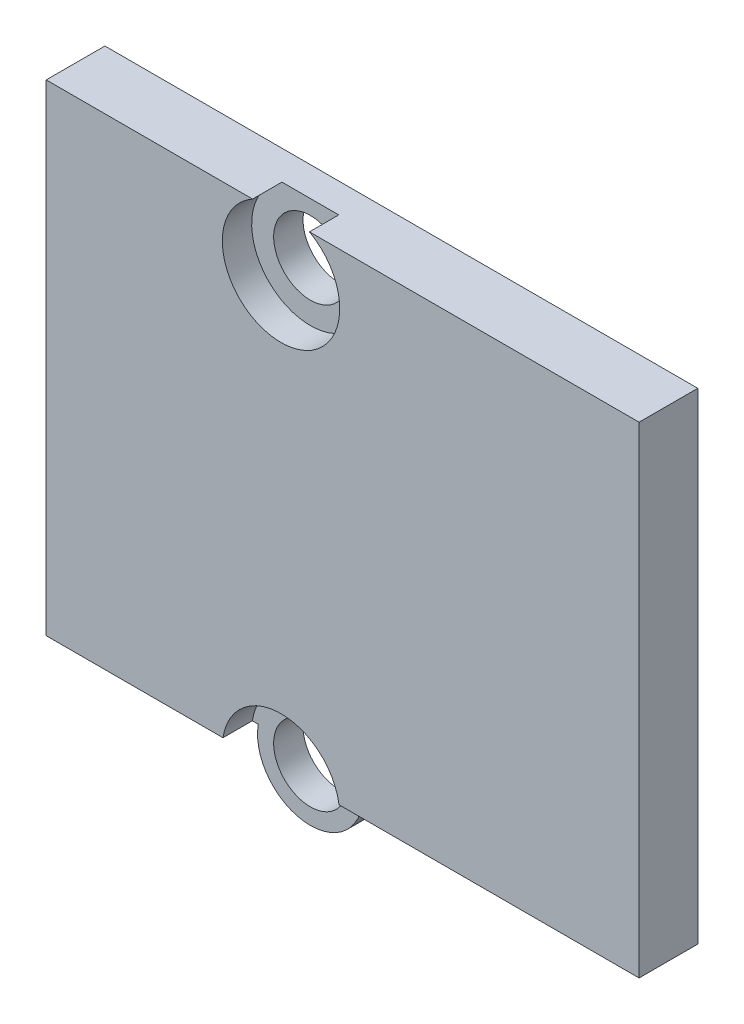
SolidWorks part; units mm, degrees
ref_plane "Plano frontal" through (0, 0, 0) normal (0, 0, 1) x (1, 0, 0)
ref_plane "Plano superior" through (0, 0, 0) normal (0, 1, 0) x (1, 0, 0)
ref_plane "Plano direito" through (0, 0, 0) normal (1, 0, 0) x (0, 0, -1)
sketch "Esboço1" plane through (0, 0, 0) normal (0, 0, 1) x (1, 0, 0)
  line L0 (12.2, 16.7) -> (-8, 16.7)
  line L1 (-8, 16.7) -> (-8, 0.3)
  line L2 (-8, 0.3) -> (-1.7748, 0.3)
  line L3 (1.7748, 0.3) -> (12.2, 0.3)
  line L4 (12.2, 0.3) -> (12.2, 16.7)
  arc A0 (-1.7748, 0.3) -> (1.7748, 0.3) centre (0, 0) ccw
  circle A1 centre (0, 0) radius 1.25
  circle A2 centre (0, 14.95) radius 1.25
  point P10 (0, 4.3257)
  point P11 (0, 0)
  point P13 (-7.2856, 16.5)
  point P14 (0, 0)
  dimension "D2" = 2.5
  dimension "D6" = 1.8
  dimension "D7" = 1.75
  dimension "D1" = 8
  dimension "D3" = 20.2
  dimension "D4" = 14.95
  dimension "D5" = 16.4
extrude "Ressalto-extrusão1" add sketch "Esboço1" along normal blind 2
sketch "Esboço2" plane through (0, 0, 2) normal (0, 0, 1) x (1, 0, 0)
  circle A0 centre (0, 14.95) radius 2
  circle A1 centre (0, 0) radius 2
  dimension "D1" = 4
extrude "Corte-extrusão1" cut sketch "Esboço2" against normal blind 1
